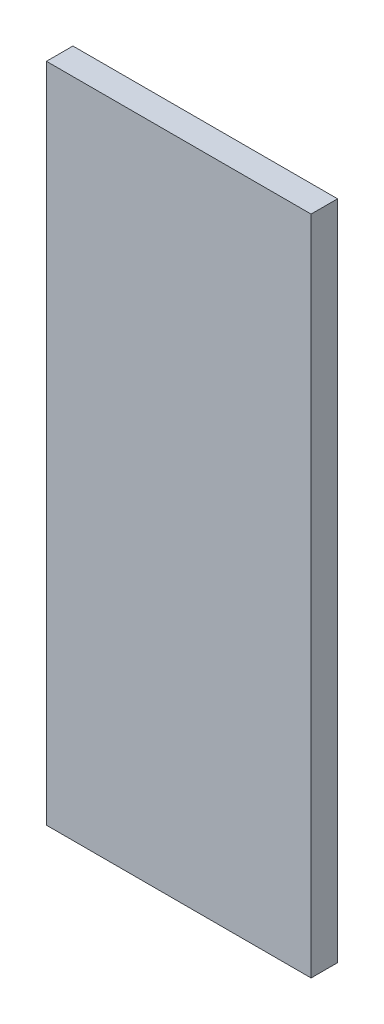
SolidWorks part; units mm, degrees
ref_plane "前视基准面" through (0, 0, 0) normal (0, 0, 1) x (1, 0, 0)
ref_plane "上视基准面" through (0, 0, 0) normal (0, 1, 0) x (1, 0, 0)
ref_plane "右视基准面" through (0, 0, 0) normal (1, 0, 0) x (0, 0, -1)
sketch "草图1" plane through (0, 0, 0) normal (0, 0, 1) x (1, 0, 0)
  line L1 (-6, -15) -> (6, -15)
  line L2 (-6, -15) -> (-6, 15)
  line L3 (-6, 15) -> (6, 15)
  line L4 (6, -15) -> (6, 15)
  line L5 (-6, -15) -> (6, 15) construction
  line L6 (-6, 15) -> (6, -15) construction
  point P0 (0, 0)
  dimension "D1" = 12
  dimension "D2" = 30
extrude "凸台-拉伸1" add sketch "草图1" along normal blind 1.2
sketch "草图5" plane through (0, 0, 0) normal (0, 0, -1) x (-1, 0, 0)
  line L1 (-2, -2.5) -> (2, -2.5)
  line L2 (-2, -2.5) -> (-2, 2.5)
  line L3 (-2, 2.5) -> (2, 2.5)
  line L4 (2, -2.5) -> (2, 2.5)
  line L5 (-2, -2.5) -> (2, 2.5) construction
  line L6 (-2, 2.5) -> (2, -2.5) construction
  point P0 (0, 0)
  dimension "D1" = 5
  dimension "D2" = 4
extrude "凸台-拉伸3" add sketch "草图5" along normal blind 2
